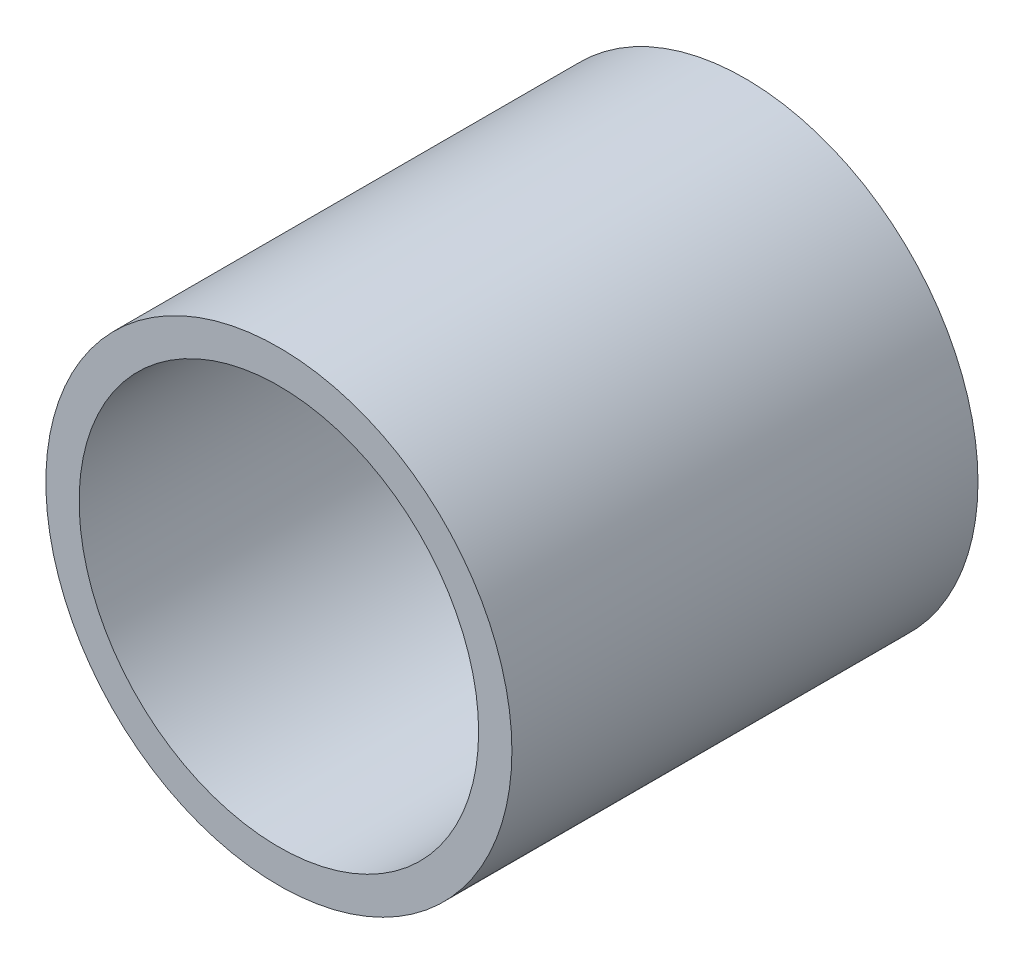
SolidWorks part; units mm, degrees
material "Alloy Steel (SS)"
ref_plane "Front Plane" through (0, 0, 0) normal (0, 0, 1) x (1, 0, 0)
ref_plane "Top Plane" through (0, 0, 0) normal (0, 1, 0) x (1, 0, 0)
ref_plane "Right Plane" through (0, 0, 0) normal (1, 0, 0) x (0, 0, -1)
sketch "Sketch1" plane through (0, 0, 0) normal (0, 0, 1) x (1, 0, 0)
  circle A0 centre (0, 0) radius 7
  circle A1 centre (0, 0) radius 6
  dimension "D1" = 14
  dimension "D2" = 1
extrude "Boss-Extrude1" add sketch "Sketch1" along normal blind 14
